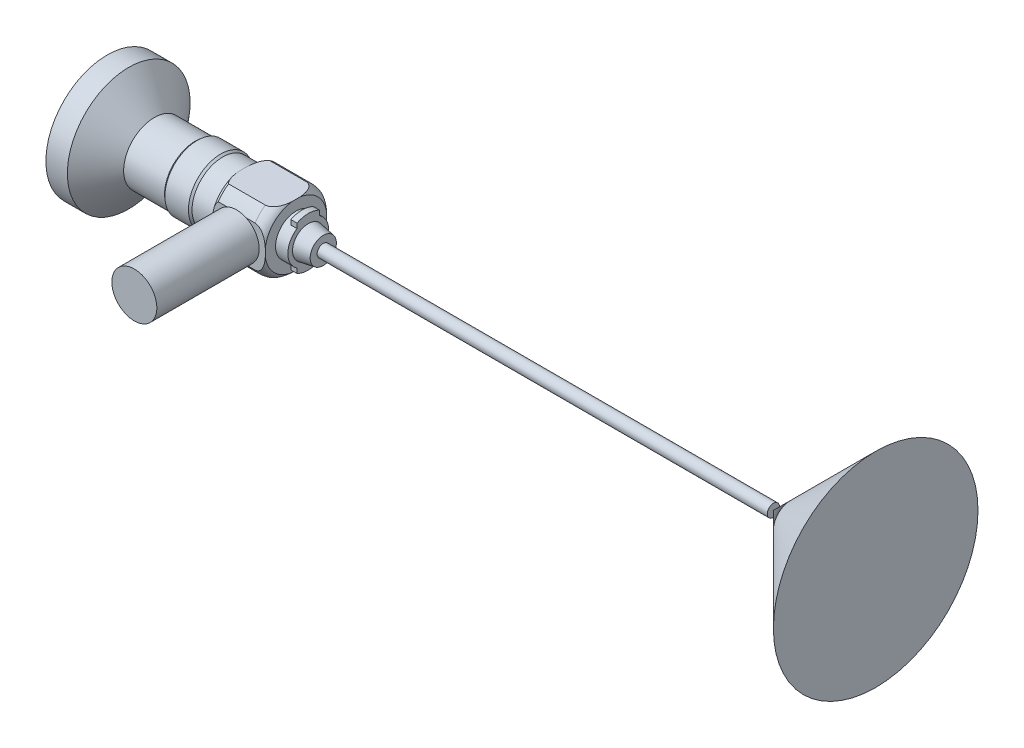
SolidWorks part; units mm, degrees
material "AISI 316 Stainless Steel Sheet (SS)"
ref_plane "Front Plane" through (0, 0, 0) normal (0, 0, 1) x (1, 0, 0)
ref_plane "Top Plane" through (0, 0, 0) normal (0, 1, 0) x (1, 0, 0)
ref_plane "Right Plane" through (0, 0, 0) normal (1, 0, 0) x (0, 0, -1)
ref_axis "Axis1" through (88.99, 0, 0) along (-1, 0, 0)
sketch "Sketch1" plane through (0, 0, 0) normal (0, 0, 1) x (1, 0, 0)
  line L0 (-74.5697, 0) -> (-77.8697, -15) construction
  line L1 (-77.8697, -15) -> (-72.6197, -15)
  line L2 (-72.6197, -15) -> (-66.3697, -7.5)
  line L3 (-66.3697, -7.5) -> (-56.3697, -7.5)
  line L4 (-56.3697, -7.5) -> (-55.8897, -7.9)
  line L5 (-55.8897, -7.9) -> (-50.1397, -7.9)
  line L6 (-50.1397, -7.9) -> (-49.6597, -7.5)
  line L7 (-49.6597, -7.5) -> (-44.6597, -7.5)
  line L8 (88.99, 0) -> (-88.99, 0) construction
  line L9 (-74.5697, 0) -> (-25.0835, 0)
  line L10 (-43.2452, -9) -> (-34.2597, -9)
  line L11 (-31.7461, -7.5592) -> (-31.7461, -5)
  line L12 (-31.7461, -5) -> (-30.2461, -5)
  line L13 (-30.2461, -5) -> (-30.2461, -6)
  line L14 (-30.2461, -6) -> (-28.7461, -6)
  line L15 (-28.7461, -6) -> (-28.7461, -3.85)
  line L16 (-28.7461, -3.85) -> (-25.0835, -3.2)
  line L17 (-25.0835, -3.2) -> (-25.0835, 0)
  arc A0 (-74.5697, 0) -> (-77.8697, -15) centre (-129.3209, 4.1823) cw
  arc A1 (-44.6597, -7.5) -> (-40.5597, -9) centre (-41.9025, -6.3168) ccw
  arc A2 (-34.2597, -9) -> (-31.7461, -7.5592) centre (-34.3096, -6) ccw
  point P12 (-40.5597, -9)
  point P16 (-34.2597, -9)
  point P17 (-44.6597, -9)
  point P18 (-37.4097, -9)
  point P20 (-30.1597, -9)
  dimension "D4" = 11.5
  dimension "D12" = 9
  dimension "D13" = 3.15
  dimension "D15" = 5
  dimension "D1" = 5.25
  dimension "D2" = 15
  dimension "D3" = 3.3
  dimension "D5" = 7.5
  dimension "D6" = 5.75
  dimension "D7" = 7.9
  dimension "D8" = 7.5
  dimension "D9" = 10
  dimension "D10" = 5
  dimension "D11" = 14.5
  dimension "D14" = 3.15
  dimension "D16" = 6
  dimension "D17" = 1.5
  dimension "D18" = 1.5
  dimension "D19" = 3.85
  dimension "D20" = 3.2
revolve "Revolve1" add sketch "Sketch1" angle 360 about axis through (88.99, 0, 0) along (-1, 0, 0)
sketch "Sketch2" plane through (-31.7461, 0, 0) normal (1, 0, 0) x (0, 0, -1)
  line L0 (0, 9) -> (0, -9)
  line L1 (12.4327, -7.5) -> (-12.4327, -7.5)
  line L2 (12.4327, -7.5) -> (12.4327, 7.5) construction
  line L3 (12.4327, 7.5) -> (-12.4327, 7.5)
  line L4 (-12.4327, -7.5) -> (-12.4327, 7.5) construction
  line L5 (12.4327, 7.5) -> (-12.4327, -7.5) construction
  line L6 (12.4327, 7.5) -> (12.4327, 11.5013)
  line L7 (12.4327, 11.5013) -> (-12.4327, 11.5013)
  line L8 (-12.4327, 11.5013) -> (-12.4327, 7.5)
  line L9 (-12.4327, -7.5) -> (-12.4327, -12.9232)
  line L10 (-12.4327, -12.9232) -> (12.4327, -12.9232)
  line L11 (12.4327, -12.9232) -> (12.4327, -7.5)
  circle A0 centre (0, 0) radius 9 construction
  circle A1 centre (0, 0) radius 9
  dimension "D1" = 15
extrude "Cut-Extrude1" cut sketch "Sketch2" against normal blind 15 contours L9 L10 L11 L1 | L8 L3 L6 L7
pattern_circular "CirPattern1" count 2 every 90 about axis through (88.99, 0, 0) along (-1, 0, 0) of "Cut-Extrude1"
sketch "Sketch3" plane through (-28.7461, 0, 0) normal (1, 0, 0) x (0, 0, -1)
  line L0 (2.75, 6.4372) -> (2.75, -6.4372) construction
  line L1 (-2.75, -6.4372) -> (-2.75, 6.4372) construction
  line L2 (2.75, -6.4372) -> (-2.75, 6.4372) construction
  line L3 (2.75, -4.1758) -> (2.75, -6.4372)
  line L4 (2.75, -6.4372) -> (-2.75, -6.4372) construction
  line L5 (-2.75, -6.4372) -> (-2.75, -4.1758)
  line L6 (2.75, 4.1758) -> (2.75, 6.4372)
  line L7 (2.75, 6.4372) -> (-2.75, 6.4372) construction
  line L8 (-2.75, 6.4372) -> (-2.75, 4.1758)
  line L9 (2.75, 6.4372) -> (6.4302, 6.4372)
  line L10 (6.4302, 6.4372) -> (5.9638, -6.4372)
  line L11 (5.9638, -6.4372) -> (2.75, -6.4372)
  line L12 (-2.75, -6.4372) -> (-6.2806, -6.4372)
  line L13 (-6.2806, -6.4372) -> (-6.2806, 6.4372)
  line L14 (-6.2806, 6.4372) -> (-2.75, 6.4372)
  circle A0 centre (0, 0) radius 6 construction
  circle A1 centre (0, 0) radius 6 construction
  arc A2 (2.75, -4.1758) -> (2.75, 4.1758) centre (0, 0) ccw
  arc A3 (-2.75, 4.1758) -> (-2.75, -4.1758) centre (0, 0) ccw
  point P3 (7, 0)
  point P4 (0, 0)
  dimension "D1" = 10
  dimension "D3" = 5.5
extrude "Cut-Extrude2" cut sketch "Sketch3" against normal up to surface (1.5 mm away) up to face at (-30.2461, 0, -6)
sketch "Sketch4" plane through (0, 0, 7.5) normal (0, 0, 1) x (1, 0, 0)
  line L0 (-34.2597, 4.9749) -> (-43.2452, -4.9749) construction
  circle A0 centre (-38.7525, 0) radius 5.5
  dimension "D1" = 11
extrude "Boss-Extrude1" add sketch "Sketch4" along normal blind 25
sketch "Sketch5" plane through (-25.0835, 0, 0) normal (1, 0, 0) x (0, 0, -1)
  circle A0 centre (0, 0) radius 1.5
  dimension "D1" = 3
extrude "Boss-Extrude2" add sketch "Sketch5" along normal blind 110
sketch "Sketch6" plane through (0, 0, 0) normal (0, 0, 1) x (1, 0, 0)
  line L0 (84.9165, 0) -> (85.1501, 0)
  line L1 (84.9165, 0) -> (109.9165, 0)
  line L2 (84.9165, -1.5) -> (84.9165, 1.5) construction
  line L3 (84.9165, -1.5) -> (84.9165, 1.5)
  line L4 (84.9165, 0) -> (109.9165, -25)
  line L5 (109.9165, -25) -> (109.9165, 0)
  dimension "D1" = 25
  dimension "D2" = 45
revolve "Revolve2" add sketch "Sketch6" angle 360 about L1
